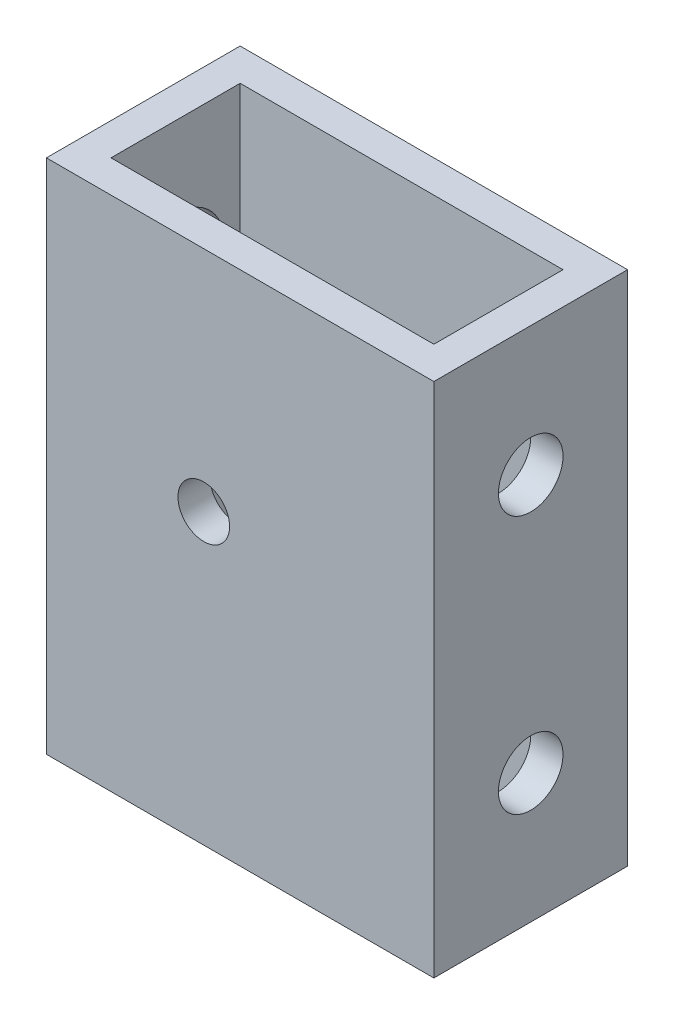
SolidWorks part; units mm, degrees
ref_plane "Front Plane" through (0, 0, 0) normal (0, 0, 1) x (1, 0, 0)
ref_plane "Top Plane" through (0, 0, 0) normal (0, 1, 0) x (1, 0, 0)
ref_plane "Right Plane" through (0, 0, 0) normal (1, 0, 0) x (0, 0, -1)
sketch "Sketch1" plane through (0, 0, 0) normal (0, 1, 0) x (1, 0, 0)
  line L0 (3.175, 15.875) -> (34.925, 15.875)
  line L1 (0, 0) -> (38.1, 0)
  line L2 (0, 0) -> (0, 19.05)
  line L3 (0, 19.05) -> (38.1, 19.05)
  line L4 (38.1, 0) -> (38.1, 19.05)
  line L5 (34.925, 3.175) -> (34.925, 15.875)
  line L6 (3.175, 3.175) -> (34.925, 3.175)
  line L7 (3.175, 3.175) -> (3.175, 15.875)
  dimension "D1" = 38.1
  dimension "D2" = 19.05
extrude "Boss-Extrude1" add sketch "Sketch1" along normal blind 50.8
sketch "Sketch2" plane through (38.1, 0, 0) normal (1, 0, 0) x (0, 0, -1)
  line L0 (9.525, 50.8) -> (9.525, 38.1) construction
  line L1 (0, 50.8) -> (19.05, 50.8) construction
  line L2 (19.05, 25.4) -> (0, 25.4) construction
  line L3 (19.05, 50.8) -> (19.05, 0) construction
  line L4 (0, 50.8) -> (0, 0) construction
  circle A0 centre (9.525, 38.1) radius 3.175
  circle A1 centre (9.525, 12.7) radius 3.175
  dimension "D1" = 6.35
  dimension "D2" = 12.7
extrude "Cut-Extrude1" cut sketch "Sketch2" against normal through all
sketch "Sketch3" plane through (0, 0, 0) normal (0, 0, 1) x (1, 0, 0)
  circle A0 centre (15.4734, 28.3956) radius 2.54 construction
  circle A1 centre (15.4734, 28.3956) radius 2.54
extrude "Cut-Extrude2" cut sketch "Sketch3" against normal through all
sketch "Sketch4" plane through (0, 0, 0) normal (-1, 0, 0) x (0, 0, 1)
  circle A0 centre (-9.525, 12.7) radius 4.7625
  circle A1 centre (-9.525, 38.1) radius 4.7625
  dimension "D1" = 9.525
extrude "Cut-Extrude3" cut sketch "Sketch4" against normal up to next
